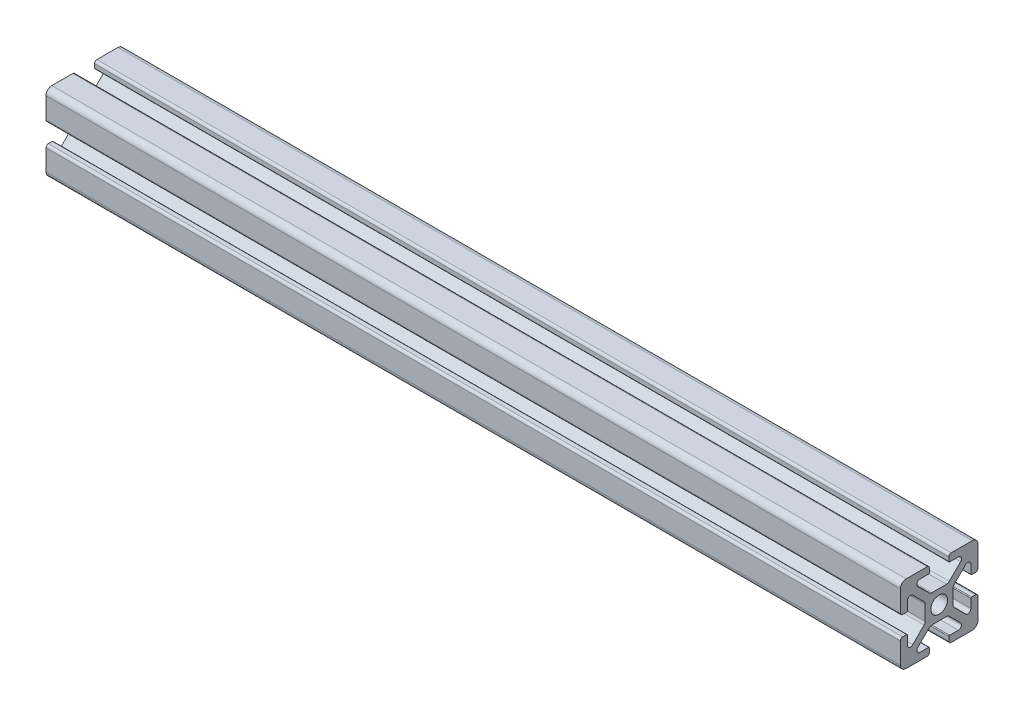
SolidWorks part; units mm, degrees
ref_plane "Front Plane" through (0, 0, 0) normal (0, 0, 1) x (1, 0, 0)
ref_plane "Top Plane" through (0, 0, 0) normal (0, 1, 0) x (1, 0, 0)
ref_plane "Right Plane" through (0, 0, 0) normal (1, 0, 0) x (0, 0, -1)
sketch "Sketch1" plane through (0, 0, 0) normal (1, 0, 0) x (0, 0, -1)
  line L0 (0, -10) -> (0, 10) construction
  line L1 (10, -10) -> (-10, -10)
  line L2 (10, -10) -> (10, 10)
  line L3 (10, 10) -> (0, 10)
  line L4 (-10, -10) -> (-10, 10)
  line L5 (10, -10) -> (-10, 10) construction
  line L6 (10, 10) -> (-10, -10) construction
  line L7 (10, 0) -> (-10, 0) construction
  line L8 (-2.5, 9.4) -> (-2.5, 8.3731)
  line L9 (-2.7, 8.1731) -> (-4.95, 8.1731)
  line L10 (-5.5157, 6.8075) -> (-2.6011, 3.8929)
  line L11 (-1.894, 3.6) -> (0, 3.6)
  line L12 (-5.3502, 4.0584) -> (-4.0584, 5.3502) construction
  line L13 (-3.825, 8.1731) -> (-3.825, 10) construction
  line L14 (-3.1, 10) -> (-10, 10)
  line L15 (-5.75, 7.3731) -> (5.75, 7.3731) construction
  circle A0 centre (0, 0) radius 2.15
  arc A1 (-4.95, 8.1731) -> (-5.5157, 6.8075) centre (-4.95, 7.3731) ccw
  arc A2 (-2.6011, 3.8929) -> (-1.894, 3.6) centre (-1.894, 4.6) ccw
  arc A3 (-2.5, 8.3731) -> (-2.7, 8.1731) centre (-2.7, 8.3731) cw
  arc A4 (-2.5, 9.4) -> (-3.1, 10) centre (-3.1, 9.4) ccw
  point P0 (0, 0)
  point P9 (0, 0)
  point P12 (0, 0)
  point P22 (-4.7043, 4.7043)
  point P32 (-2.5, 10)
  point P33 (-2.5, 8.8866)
  point P35 (-4.0584, 5.3502)
  point P37 (0, 7.3731)
  dimension "Center Hole Diameter" = 4.3
  dimension "D4" = 1
  dimension "D5" = 0.2
  dimension "D6" = 0.6
  dimension "D3" = 0.8
  dimension "Rail Height" = 20
  dimension "D7" = 6.4
  dimension "T Slot Width" = 5
  dimension "D10" = 10
  dimension "Rail Width" = 20
  dimension "D2" = 11.5
sketch "Sketch2" plane through (0, 0, 0) normal (0, 0, 1) x (1, 0, 0)
  line L0 (-132.4, 10) -> (-132.4, -10) construction
  line L1 (152.4, -10) -> (-152.4, -10) construction
  line L2 (152.4, -10) -> (152.4, 10) construction
  line L3 (152.4, 10) -> (-152.4, 10) construction
  line L4 (-152.4, -10) -> (-152.4, 10) construction
  line L5 (152.4, -10) -> (-152.4, 10) construction
  line L6 (152.4, 10) -> (-152.4, -10) construction
  line L7 (132.4, 10) -> (132.4, -10) construction
  point P0 (0, 0)
  point P12 (132.4, 0)
  dimension "Length" = 304.8
  dimension "D1" = 20
  dimension "D2" = 20
sketch "Sketch3" plane through (0, 0, 0) normal (1, 0, 0) x (0, 0, -1)
  line L0 (-5.5157, 6.8075) -> (-2.6011, 3.8929) construction
  line L5 (-3.1, 10) -> (-10, 10) construction
  line L6 (-2.5, 9.4) -> (-2.5, 8.3731) construction
  line L7 (-2.7, 8.1731) -> (-4.95, 8.1731) construction
  line L8 (-1.894, 3.6) -> (0, 3.6) construction
  line L9 (-5.5157, 6.8075) -> (-2.6011, 3.8929)
  line L10 (-10, 10) -> (0, 0) construction
  line L12 (-3.6, 1.894) -> (-3.6, 0)
  line L13 (-8.1731, 2.7) -> (-8.1731, 4.95)
  line L14 (-3.1, 10) -> (-8.5, 10)
  line L15 (-2.5, 9.4) -> (-2.5, 8.3731)
  line L16 (-2.7, 8.1731) -> (-4.95, 8.1731)
  line L17 (-1.894, 3.6) -> (0, 3.6)
  line L18 (-9.4, 2.5) -> (-8.3731, 2.5)
  line L19 (-10, 3.1) -> (-10, 8.5)
  line L20 (-6.8075, 5.5157) -> (-3.8929, 2.6011)
  line L21 (-3.6, 0) -> (-2.15, 0)
  line L22 (0, 3.6) -> (0, 2.15)
  arc A0 (-2.5, 9.4) -> (-3.1, 10) centre (-3.1, 9.4) ccw construction
  arc A1 (-2.7, 8.1731) -> (-2.5, 8.3731) centre (-2.7, 8.3731) ccw construction
  arc A2 (-4.95, 8.1731) -> (-5.5157, 6.8075) centre (-4.95, 7.3731) ccw construction
  arc A3 (-2.6011, 3.8929) -> (-1.894, 3.6) centre (-1.894, 4.6) ccw construction
  arc A4 (-2.5, 9.4) -> (-3.1, 10) centre (-3.1, 9.4) ccw
  arc A5 (-2.7, 8.1731) -> (-2.5, 8.3731) centre (-2.7, 8.3731) ccw
  arc A6 (-4.95, 8.1731) -> (-5.5157, 6.8075) centre (-4.95, 7.3731) ccw
  arc A7 (-2.6011, 3.8929) -> (-1.894, 3.6) centre (-1.894, 4.6) ccw
  arc A8 (-3.8929, 2.6011) -> (-3.6, 1.894) centre (-4.6, 1.894) cw
  arc A9 (-8.1731, 4.95) -> (-6.8075, 5.5157) centre (-7.3731, 4.95) cw
  arc A10 (-8.1731, 2.7) -> (-8.3731, 2.5) centre (-8.3731, 2.7) cw
  arc A11 (-9.4, 2.5) -> (-10, 3.1) centre (-9.4, 3.1) cw
  circle A12 centre (0, 0) radius 2.15 construction
  arc A13 (0, 2.15) -> (-2.15, 0) centre (0, 0) ccw
  arc A14 (-10, 8.5) -> (-8.5, 10) centre (-8.5, 8.5) cw
  dimension "D1" = 1.5
extrude "Boss-Extrude1" add sketch "Sketch3" against normal blind 220
mirror "Mirror1" about plane through (0, 0, 0) normal (0, 1, 0) of bodies 104
mirror "Mirror2" about plane through (0, 0, 0) normal (0, 0, 1) of bodies 105
equation "\"D10@Sketch1\" = \"Rail Height@Sketch1\" / 2"
equation "\"D2@Sketch2\"=\"D1@Sketch2\""
